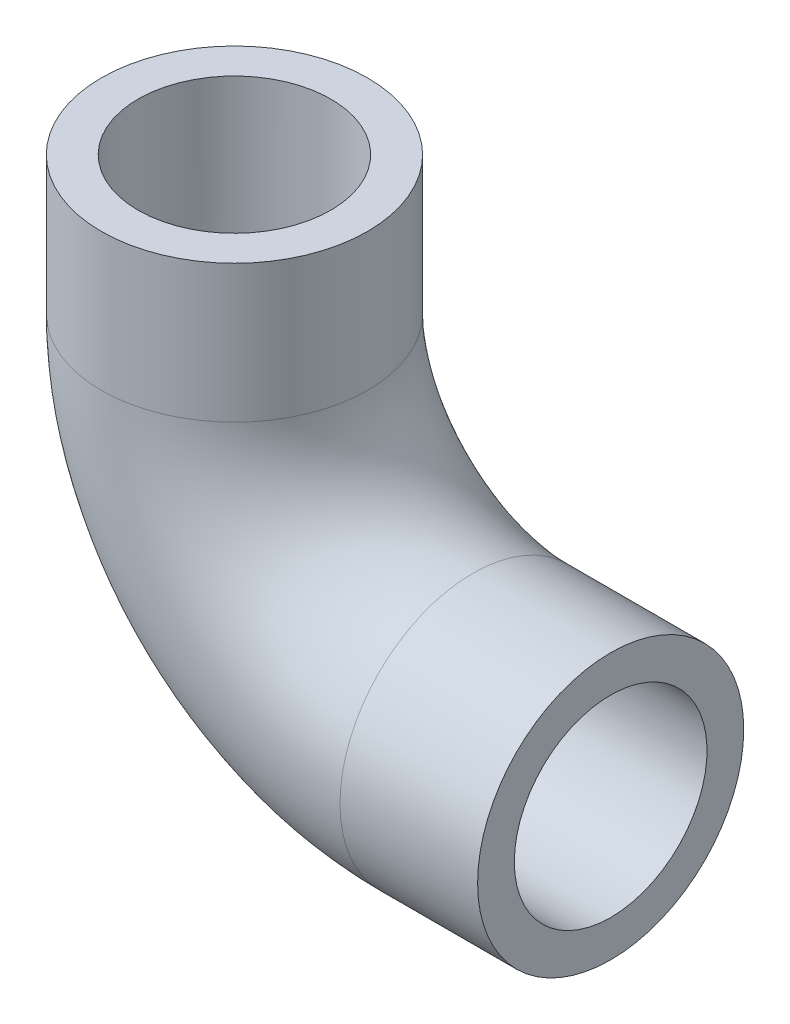
SolidWorks part; units mm, degrees
ref_plane "Front Plane" through (0, 0, 0) normal (0, 0, 1) x (1, 0, 0)
ref_plane "Top Plane" through (0, 0, 0) normal (0, 1, 0) x (1, 0, 0)
ref_plane "Right Plane" through (0, 0, 0) normal (1, 0, 0) x (0, 0, -1)
sketch "Sketch1" plane through (0, 0, 0) normal (0, 0, 1) x (1, 0, 0)
  line L0 (0, 0) -> (0, -150)
  line L1 (260, -410) -> (410, -410)
  arc A0 (0, -150) -> (260, -410) centre (260, -150) ccw
sketch "Sketch2" plane through (0, 0, 0) normal (0, 1, 0) x (1, 0, 0)
  circle A0 centre (0, 0) radius 145
  circle A1 centre (0, 0) radius 105
sweep "Sweep1" add profiles "Sketch2" path "Sketch1"
